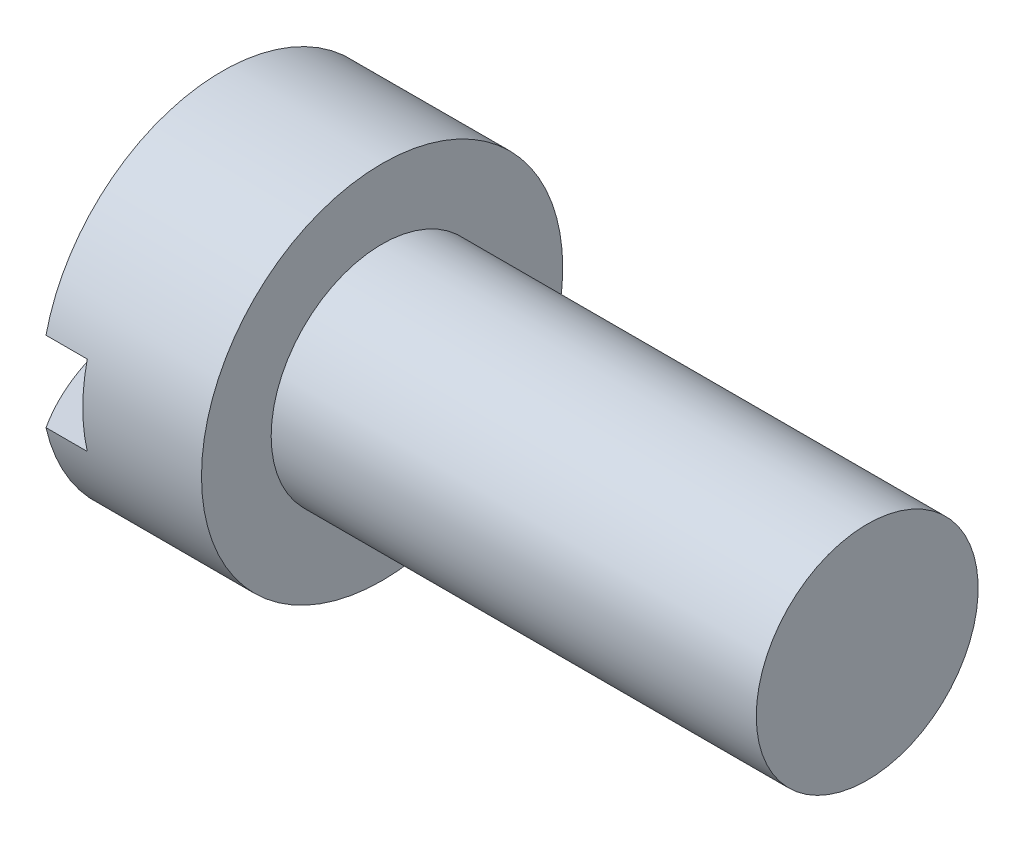
SolidWorks part; units mm, degrees
ref_plane "Plane1" through (0, 0, 0) normal (0, 0, 1) x (1, 0, 0)
ref_plane "Plane2" through (0, 0, 0) normal (0, 1, 0) x (1, 0, 0)
ref_plane "Plane3" through (0, 0, 0) normal (1, 0, 0) x (0, 0, -1)
sketch "BodySke" plane through (0, 0, 0) normal (0, 0, 1) x (1, 0, 0)
  line L0 (2.1082, 1.0922) -> (2.1082, 1.778)
  line L1 (2.1082, 1.778) -> (0.5334, 1.778)
  line L2 (-9.6035, 0) -> (16.6589, 0) construction
  line L3 (6.8834, 0) -> (0, 0)
  line L4 (2.1082, 1.0922) -> (6.8834, 1.0922)
  line L5 (6.8834, 1.0922) -> (6.8834, 0)
  line L6 (2.1082, -1.778) -> (0.5334, -1.778) construction
  line L7 (2.1082, -1.0922) -> (6.8834, -1.0922) construction
  line L8 (2.5629, 1.2192) -> (2.5629, -0.4698) construction
  line L9 (2.1082, 1.2192) -> (2.1082, -0.4698) construction
  arc A0 (0, 0) -> (0.5334, 1.778) centre (3.23, 0) cw
  dimension "Head_ht" = 2.1082
  dimension "Diameter" = 2.1844
  dimension "Length" = 4.7752
  dimension "Head_dia" = 3.556
  dimension "Head_side_ht" = 1.5748
  dimension "Advance" = 0.4547
  dimension "Thread_nom" = 4.7752
revolve "Base-Revolve" add sketch "BodySke" angle 360 about L2
cosmetic thread "ThreadCosmetic" [suppressed] parameters "Thread_length"=4.3205, "Thread_minor"=1.6459
sketch "Sketch2" plane through (0, 0, 0) normal (1, 0, 0) x (0, 0, -1)
  line L0 (-1.778, -0.3937) -> (-1.778, 0.3937)
  line L1 (-1.778, 0.3937) -> (1.778, 0.3937)
  line L2 (1.778, 0.3937) -> (1.778, -0.3937)
  line L3 (1.778, -0.3937) -> (-1.778, -0.3937)
  dimension "D1" = 3.556
  dimension "D2" = 1.778
  dimension "D3" = 0.3937
  dimension "Slot_width" = 0.7874
extrude "Slot" cut sketch "Sketch2" along normal blind 0.9398
sketch "Sketch3" plane through (0, 0, 0) normal (1, 0, 0) x (0, 0, -1)
  line L0 (0.3048, -1.3335) -> (-0.3048, -1.3335)
  line L1 (0.3048, -1.3335) -> (0.3048, 1.3335)
  line L2 (-0.3048, 1.3335) -> (0.3048, 1.3335)
  line L3 (-0.3048, 1.3335) -> (-0.3048, -1.3335)
  dimension "D1" = 0.3048
  dimension "Cross_width" = 0.6096
  dimension "D2" = 1.3335
  dimension "Cross_dia" = 2.667
ref_plane "Plane4" through (1.4224, 0, 0) normal (1, 0, 0) x (0, 0, -1)
sketch "Sketch4" plane through (1.4224, 0, 0) normal (1, 0, 0) x (0, 0, -1)
  line L0 (0.1524, -0.1524) -> (-0.1524, -0.1524)
  line L1 (0.1524, -0.1524) -> (0.1524, 0.1524)
  line L2 (-0.1524, 0.1524) -> (0.1524, 0.1524)
  line L3 (-0.1524, 0.1524) -> (-0.1524, -0.1524)
  dimension "D1" = 0.3048
  dimension "D2" = 0.1524
  dimension "D3" = 0.3048
  dimension "D4" = 0.1524
loft "Cross" [suppressed] cut profiles "Sketch3", "Sketch4"
pattern_circular "CirPattern1" [suppressed] count 2 every 90 about axis through (-9.6035, 0, 0) along (1, 0, 0)
sketch "Sketch5" plane through (0, 0, 0) normal (0, 1, 0) x (1, 0, 0)
  line L4 (-9.6035, 0) -> (16.6589, 0) construction
  line L5 (2.1082, -6.312) -> (2.1082, 6.3337) construction
  circle A0 centre (1.4478, 0) radius 0.3937
  dimension "Drilled_hole_dia" = 0.7874
  dimension "D1" = 2.1082
  dimension "Drilled_hole_loc" = 0.6604
extrude "Hole" [suppressed] cut sketch "Sketch5" against normal through all and the other way through all
sketch "ThdSchSke" plane through (0, 0, 0) normal (0, 0, 1) x (1, 0, 0)
  line L0 (2.5629, -0.823) -> (2.3743, -1.0922)
  line L1 (2.5629, -0.823) -> (2.7514, -1.0922)
  line L2 (2.7514, -1.0922) -> (2.7514, -1.3653)
  line L3 (-3.175, 0) -> (5.1513, 0) construction
  line L5 (2.7514, -1.3653) -> (2.3743, -1.3653)
  line L6 (2.3743, -1.3653) -> (2.3743, -1.0922)
  dimension "Thread_minor" = 1.6459
  dimension "Diameter" = 2.1844
  dimension "Start" = 2.5629
  dimension "SideAngle" = 55
  dimension "VeeAngle" = 70
  dimension "Overcut" = 2.7305
revolve "ThreadSchematic" [suppressed] cut sketch "ThdSchSke" angle 360 about L3
pattern_linear "ThdSchPat" [suppressed]
equation "\"D1@Sketch3\" = \"Cross_width@Sketch3\" / 2"
equation "\"D2@Sketch3\" = \"Cross_dia@Sketch3\" / 2"
equation "\"D1@Sketch4\" = \"Cross_width@Sketch3\"*.5"
equation "\"D2@Sketch4\" = \"D1@Sketch4\" / 2"
equation "\"D3@Sketch4\" = \"D1@Sketch4\""
equation "\"D4@Sketch4\" = \"D2@Sketch4\""
equation "\"D1@Sketch2\" = \"Head_dia@BodySke\""
equation "\"D2@Sketch2\" = \"D1@Sketch2\" / 2"
equation "\"D3@Sketch2\" = \"Slot_width@Sketch2\" / 2"
equation "\"D1@Sketch5\" = \"Head_ht@BodySke\""
equation "\"Thread_length@ThreadCosmetic\" = ((sgn( (\"Length@BodySke\" - \"Advance@BodySke\" ) - \"Thread_nom@BodySke\" )-1)*( (\"Length@BodySke\" - \"Advance@BodySke\" ) - \"Thread_nom@BodySke\" ))/-2+ \"Thread_nom@BodySke\""
equation "\"Thread_minor@ThdSchSke\" = \"Thread_minor@ThreadCosmetic\""
equation "\"Diameter@ThdSchSke\" = \"Diameter@BodySke\""
equation "\"Overcut@ThdSchSke\" = \"Diameter@BodySke\" * 1.25"
equation "\"Start@ThdSchSke\" = \"Head_ht@BodySke\" + \"Length@BodySke\" - \"Thread_length@ThreadCosmetic\"  '---Non-countersunk---"
equation "\"Num_threads@ThdSchPat\" = int( \"Thread_length@ThreadCosmetic\" / \"Advance@BodySke\" + 0.999 )  + 1"
equation "\"Advance@ThdSchPat\" = \"Thread_length@ThreadCosmetic\" /  (\"Num_threads@ThdSchPat\" - 1) 'relax it"
